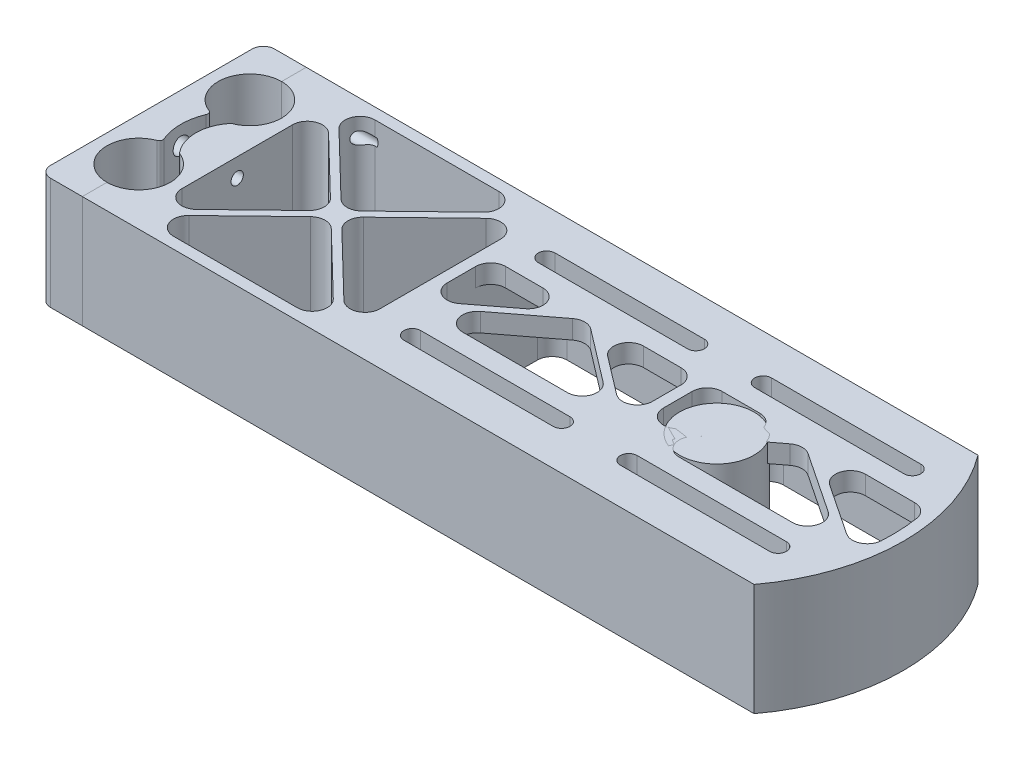
SolidWorks part; units mm, degrees
material "Сплав 2024"
ref_plane "Front" through (0, 0, 0) normal (0, 0, 1) x (1, 0, 0)
ref_plane "Top" through (0, 0, 0) normal (0, 1, 0) x (1, 0, 0)
ref_plane "Right" through (0, 0, 0) normal (1, 0, 0) x (0, 0, -1)
sketch "Эскиз1" plane through (0, 0, 0) normal (0, 1, 0) x (1, 0, 0)
  line L0 (0, 0) -> (0, 60) construction
  line L1 (0, 60) -> (180, 60)
  line L2 (190, 60) -> (190, 0) construction
  line L3 (190, 0) -> (180, 0) construction
  line L4 (0, 30) -> (140, 30) construction
  line L5 (0, 60) -> (0, 52)
  line L6 (0, 37.8) -> (0, 22.2)
  line L7 (0, 8) -> (0, 0)
  line L8 (140, 30) -> (190, 30) construction
  line L9 (180, 60) -> (190, 60) construction
  line L10 (180, 0) -> (0, 0)
  circle A0 centre (0, 44.9) radius 7.1 construction
  circle A1 centre (0, 15.1) radius 7.1 construction
  arc A2 (0, 52) -> (0, 37.8) centre (0, 44.9) cw
  arc A3 (0, 8) -> (0, 22.2) centre (0, 15.1) ccw
  arc A4 (180, 0) -> (180, 60) centre (140, 30) ccw
  point P11 (0, 52)
  point P12 (0, 37.8)
  dimension "D2" = 14.2
  dimension "D4" = 29.8
  dimension "D8" = 50
  dimension "D1" = 60
  dimension "D3" = 15.1
  dimension "D5" = 140
  dimension "D6" = 50
  dimension "D7" = 190
extrude "Бобышка-Вытянуть1" add sketch "Эскиз1" along normal blind 30
sketch "Эскиз2" plane through (0, 30, 0) normal (0, 1, 0) x (1, 0, 0)
  line L5 (3, 3) -> (178.4708, 3)
  line L6 (3, 3) -> (178.4708, 3)
  line L12 (3, 5.4558) -> (3, 3)
  line L15 (178.4708, 57) -> (3, 57)
  line L16 (3, 57) -> (3, 54.5442)
  line L17 (3, 35.2558) -> (3, 24.7442)
  line L18 (3, 5.4558) -> (3, 3)
  line L21 (178.4708, 57) -> (3, 57)
  line L22 (3, 57) -> (3, 54.5442)
  line L23 (3, 35.2558) -> (3, 24.7442)
  arc A3 (178.4708, 3) -> (178.4708, 57) centre (140, 30) ccw
  arc A4 (3, 35.2558) -> (3, 54.5442) centre (0, 44.9) ccw
  arc A5 (3, 5.4558) -> (3, 24.7442) centre (0, 15.1) ccw
  arc A6 (3, 35.2558) -> (3, 54.5442) centre (0, 44.9) ccw
  arc A7 (3, 5.4558) -> (3, 24.7442) centre (0, 15.1) ccw
  arc A8 (178.4708, 3) -> (178.4708, 57) centre (140, 30) ccw
  dimension "D1" = 3
extrude "Вырез-Вытянуть1" cut sketch "Эскиз2" against normal through all
sketch "Temp" plane through (0, 30, 0) normal (0, 1, 0) x (1, 0, 0)
  circle A0 centre (140, 30) radius 10
  dimension "D1" = 20
extrude "Бобышка-Вытянуть2" add sketch "Temp" against normal up to surface (30 mm away) separate body up to face at (49.7088, 0, -30)
sketch "Эскиз3" plane through (0, 30, 0) normal (0, 1, 0) x (1, 0, 0)
  line L0 (178.4708, 57) -> (3, 57) construction
  line L1 (174.4166, 48) -> (134.4166, 48) construction
  line L2 (174.4166, 43.5) -> (134.4166, 43.5)
  line L3 (174.4166, 52.5) -> (134.4166, 52.5)
  line L4 (174.4166, 48) -> (183.4166, 48) construction
  line L5 (125.4166, 57) -> (125.4166, 30) construction
  line L6 (0, 30) -> (140, 30) construction
  line L7 (76.4166, 48) -> (116.4166, 48) construction
  line L8 (76.4166, 43.5) -> (116.4166, 43.5)
  line L9 (76.4166, 52.5) -> (116.4166, 52.5)
  line L10 (187, 30) -> (125.4166, 30) construction
  line L11 (76.4166, 12) -> (116.4166, 12) construction
  line L12 (76.4166, 16.5) -> (116.4166, 16.5)
  line L13 (76.4166, 7.5) -> (116.4166, 7.5)
  line L14 (174.4166, 12) -> (134.4166, 12) construction
  line L15 (174.4166, 16.5) -> (134.4166, 16.5)
  line L16 (174.4166, 7.5) -> (134.4166, 7.5)
  line L17 (68.9166, 57) -> (68.9166, 40.5)
  line L18 (68.9166, 40.5) -> (185.8121, 40.5)
  line L19 (178.4708, 57) -> (68.9166, 57)
  line L20 (76.4166, 12) -> (116.4166, 12) construction
  line L21 (76.4166, 16.5) -> (116.4166, 16.5)
  line L22 (76.4166, 7.5) -> (116.4166, 7.5)
  line L23 (174.4166, 12) -> (134.4166, 12) construction
  line L24 (174.4166, 16.5) -> (134.4166, 16.5)
  line L25 (174.4166, 7.5) -> (134.4166, 7.5)
  line L26 (68.9166, 19.5) -> (185.8121, 19.5)
  line L27 (178.4708, 3) -> (68.9166, 3)
  line L28 (68.9166, 3) -> (68.9166, 19.5)
  arc A0 (174.4166, 43.5) -> (174.4166, 52.5) centre (174.4166, 48) ccw
  arc A1 (134.4166, 52.5) -> (134.4166, 43.5) centre (134.4166, 48) ccw
  arc A2 (178.4708, 3) -> (178.4708, 57) centre (140, 30) ccw construction
  arc A3 (76.4166, 43.5) -> (76.4166, 52.5) centre (76.4166, 48) cw
  arc A4 (116.4166, 52.5) -> (116.4166, 43.5) centre (116.4166, 48) cw
  arc A5 (76.4166, 16.5) -> (76.4166, 7.5) centre (76.4166, 12) ccw
  arc A6 (116.4166, 7.5) -> (116.4166, 16.5) centre (116.4166, 12) ccw
  arc A7 (174.4166, 16.5) -> (174.4166, 7.5) centre (174.4166, 12) cw
  arc A8 (134.4166, 7.5) -> (134.4166, 16.5) centre (134.4166, 12) cw
  arc A9 (185.8121, 40.5) -> (178.4708, 57) centre (140, 30) ccw
  arc A10 (76.4166, 16.5) -> (76.4166, 7.5) centre (76.4166, 12) ccw
  arc A11 (116.4166, 7.5) -> (116.4166, 16.5) centre (116.4166, 12) ccw
  arc A12 (174.4166, 16.5) -> (174.4166, 7.5) centre (174.4166, 12) cw
  arc A13 (134.4166, 7.5) -> (134.4166, 16.5) centre (134.4166, 12) cw
  arc A14 (185.8121, 19.5) -> (178.4708, 3) centre (140, 30) cw
  point P1 (154.4166, 48)
  point P20 (96.4166, 48)
  point P28 (96.4166, 12)
  point P35 (154.4166, 12)
  arc M3 (178.4708, 57) -> (178.4708, 3) centre (140, 30) cw
  line M4 (178.4708, 3) -> (3, 3)
  line M10 (3, 57) -> (178.4708, 57)
  dimension "D1" = 4.5
  dimension "D6" = 3
  dimension "D2" = 40
  dimension "D3" = 9
  dimension "D4" = 9
  dimension "D5" = 9
  dimension "D7" = 7.5
extrude "Бобышка-Вытянуть3" add sketch "Эскиз3" against normal blind 5 contours L17 L18 A1 L3 A0 L2 L9 A4 L8 A3 M3 M10 | L28 L26 A6 L13 A5 L12 L16 A8 L15 A7 M4 M3
sketch "Эскиз4" plane through (0, 30, 0) normal (0, 1, 0) x (1, 0, 0)
  line L0 (3, 57) -> (3, 54.5442) construction
  line L1 (3, 35.2558) -> (3, 24.7442) construction
  line L2 (3, 5.4558) -> (3, 3) construction
  line L3 (3, 3) -> (68.9166, 3) construction
  line L4 (68.9166, 57) -> (3, 57) construction
  line L5 (3, 57) -> (3, 54.5442)
  line L6 (3, 35.2558) -> (3, 24.7442)
  line L7 (3, 5.4558) -> (3, 3)
  line L8 (3, 3) -> (10.1, 3)
  line L9 (10.1, 57) -> (3, 57)
  line L10 (10.1, 57) -> (10.1, 3)
  arc A0 (3, 35.2558) -> (3, 54.5442) centre (0, 44.9) ccw construction
  arc A1 (3, 5.4558) -> (3, 24.7442) centre (0, 15.1) ccw construction
  arc A2 (3, 35.2558) -> (3, 54.5442) centre (0, 44.9) ccw
  arc A3 (3, 5.4558) -> (3, 24.7442) centre (0, 15.1) ccw
  line M4 (68.9166, 3) -> (3, 3)
  line M5 (3, 3) -> (3, 5.4558)
  arc M6 (3, 5.4558) -> (3, 24.7442) centre (0, 15.1) ccw
  line M7 (3, 24.7442) -> (3, 35.2558)
  arc M8 (3, 35.2558) -> (3, 54.5442) centre (0, 44.9) ccw
  line M9 (3, 54.5442) -> (3, 57)
  line M10 (3, 57) -> (68.9166, 57)
extrude "Бобышка-Вытянуть4" add sketch "Эскиз4" against normal through all contours L10 M10 M9 M8 | L10 M8 M7 M6 | L10 M6 M5 M4
sketch "Эскиз6" plane through (0, 30, 0) normal (0, 1, 0) x (1, 0, 0)
  line L0 (65.9166, 57) -> (65.9166, 3)
  line L1 (68.9166, 57) -> (10.1, 57) construction
  line L2 (10.1, 3) -> (68.9166, 3) construction
  line L3 (68.9166, 57) -> (68.9166, 40.5) construction
  line L4 (65.9166, 3) -> (68.9166, 3)
  line L5 (68.9166, 3) -> (68.9166, 57)
  line L6 (68.9166, 57) -> (65.9166, 57)
  dimension "D1" = 3
extrude "Бобышка-Вытянуть5" add sketch "Эскиз6" against normal through all
sketch "Эскиз7" plane through (0, 30, 0) normal (0, 1, 0) x (1, 0, 0)
  line L0 (10.1, 3) -> (65.9166, 57) construction
  line L1 (10.1, 57) -> (65.9166, 3) construction
  line L2 (10.1, 55.6086) -> (36.5701, 30)
  line L3 (11.5382, 3) -> (38.0083, 28.6086)
  line L4 (11.5382, 57) -> (38.0083, 31.3914)
  line L5 (10.1, 4.3914) -> (36.5701, 30)
  line L6 (65.9166, 57) -> (10.1, 57) construction
  line L7 (10.1, 57) -> (10.1, 3) construction
  line L8 (10.1, 3) -> (65.9166, 3) construction
  line L9 (65.9166, 57) -> (65.9166, 3) construction
  line L10 (65.9166, 57) -> (64.4784, 57)
  line L11 (10.1, 57) -> (10.1, 55.6086)
  line L12 (10.1, 3) -> (11.5382, 3)
  line L13 (65.9166, 57) -> (65.9166, 55.6086)
  line L14 (11.5382, 57) -> (10.1, 57)
  line L15 (10.7953, 57.7187) -> (66.6119, 3.7187) construction
  line L16 (9.4047, 56.2813) -> (65.2213, 2.2813) construction
  line L17 (65.9166, 4.3914) -> (65.9166, 3)
  line L18 (9.4047, 3.7187) -> (65.2213, 57.7187) construction
  line L19 (10.7953, 2.2813) -> (66.6119, 56.2813) construction
  line L20 (64.4784, 3) -> (65.9166, 3)
  line L21 (10.1, 4.3914) -> (10.1, 3)
  line L22 (39.4465, 30) -> (65.9166, 55.6086)
  line L23 (39.4465, 30) -> (65.9166, 4.3914)
  line L24 (38.0083, 31.3914) -> (64.4784, 57)
  line L25 (38.0083, 28.6086) -> (64.4784, 3)
  dimension "D1" = 1
  dimension "D2" = 1
extrude "Бобышка-Вытянуть6" add sketch "Эскиз7" against normal through all
sketch "Эскиз9" plane through (0, 25, 0) normal (0, -1, 0) x (1, 0, 0)
  line L0 (120.9166, -12) -> (129.9166, -12) construction
  line L1 (125.4166, -3) -> (125.4166, -57) construction
  line L2 (68.9166, -57) -> (178.4708, -57) construction
  line L3 (123.9166, -3) -> (123.9166, -57)
  line L4 (101.5292, -3) -> (68.9166, -3) construction
  line L5 (126.9166, -3) -> (126.9166, -57)
  line L6 (123.9166, -3) -> (126.9166, -3)
  line L7 (123.9166, -57) -> (126.9166, -57)
  arc A0 (116.4166, -16.5) -> (116.4166, -7.5) centre (116.4166, -12) ccw construction
  arc A1 (134.4166, -16.5) -> (134.4166, -7.5) centre (134.4166, -12) ccw construction
  point P8 (125.4166, -12)
  dimension "D1" = 1.5
  dimension "D2" = 1.5
extrude "Бобышка-Вытянуть8" add sketch "Эскиз9" along normal through all and the other way through all
sketch "Эскиз8" plane through (0, 30, 0) normal (0, 1, 0) x (1, 0, 0)
  line L0 (96.4166, 43.5) -> (96.4166, 16.5) construction
  line L1 (76.4166, 43.5) -> (116.4166, 43.5) construction
  line L2 (76.4166, 16.5) -> (116.4166, 16.5) construction
  line L3 (154.4166, 43.5) -> (154.4166, 16.5) construction
  line L4 (174.4166, 43.5) -> (134.4166, 43.5) construction
  line L5 (174.4166, 16.5) -> (134.4166, 16.5) construction
  line L6 (68.9166, 19.5) -> (96.4166, 40.5) construction
  line L7 (116.4166, 48) -> (134.4166, 48) construction
  line L8 (125.4166, 48) -> (125.4166, 19.5) construction
  line L9 (68.9166, 40.5) -> (123.9166, 40.5) construction
  line L10 (96.4166, 40.5) -> (123.9166, 19.5) construction
  line L11 (126.9166, 19.5) -> (154.4401, 40.4052) construction
  line L12 (154.4401, 40.4052) -> (185.8121, 19.5) construction
  line L13 (70.5643, 19.5) -> (96.4166, 39.2418)
  line L14 (96.4166, 39.2418) -> (122.2689, 19.5)
  line L15 (128.5699, 19.5) -> (154.478, 39.1782)
  line L16 (154.478, 39.1782) -> (184.0088, 19.5)
  line L17 (68.9166, 20.7582) -> (94.7689, 40.5)
  line L18 (98.0643, 40.5) -> (123.9166, 20.7582)
  line L19 (126.9166, 20.7557) -> (152.9116, 40.5)
  line L20 (122.2689, 19.5) -> (123.9166, 19.5)
  line L22 (94.7689, 40.5) -> (98.0643, 40.5)
  line L23 (68.9166, 19.5) -> (68.9166, 40.5) construction
  line L24 (68.9166, 19.5) -> (123.9166, 19.5) construction
  line L25 (123.9166, 19.5) -> (123.9166, 40.5) construction
  line L26 (126.9166, 40.5) -> (126.9166, 19.5) construction
  line L27 (126.9166, 40.5) -> (185.8121, 40.5) construction
  line L28 (126.9166, 19.5) -> (185.8121, 19.5) construction
  line L29 (68.9166, 19.5) -> (68.9166, 20.7582)
  line L30 (68.9166, 19.5) -> (70.5643, 19.5)
  line L31 (123.9166, 19.5) -> (123.9166, 20.7582)
  line L32 (126.9166, 20.7557) -> (126.9166, 19.5)
  line L33 (152.9116, 40.5) -> (156.1011, 40.5)
  line L34 (126.9166, 19.5) -> (128.5699, 19.5)
  line L35 (184.0088, 19.5) -> (185.8121, 19.5)
  line L36 (154.4021, 41.6321) -> (186.3666, 20.3322) construction
  line L37 (154.478, 39.1782) -> (185.2576, 18.6678) construction
  line L38 (156.1011, 40.5) -> (186.0401, 20.5497)
  line L39 (127.5214, 18.7037) -> (154.478, 39.1782) construction
  line L40 (126.3117, 20.2963) -> (154.4021, 41.6321) construction
  line L42 (96.4166, 41.7582) -> (124.5235, 20.2948) construction
  line L43 (68.3097, 20.2948) -> (96.4166, 41.7582) construction
  line L44 (69.5235, 18.7052) -> (96.4166, 39.2418) construction
  line L45 (96.4166, 39.2418) -> (123.3097, 18.7052) construction
  arc A1 (185.8121, 19.5) -> (185.8121, 40.5) centre (140, 30) ccw construction
  arc A2 (185.8121, 19.5) -> (186.0401, 20.5497) centre (140, 30) ccw
  point P26 (69.5235, 18.7052)
  point P27 (96.4324, 39.2539)
  point P28 (125.4324, 18.2539)
  point P30 (185.2357, 18.6828)
  point P31 (68.3097, 20.2948)
  point P32 (96.4007, 41.7461)
  point P33 (125.4007, 20.7461)
  point P34 (154.3931, 42.8858)
  point P35 (186.3885, 20.3172)
  point P49 (154.4166, 40.5)
  dimension "D1" = 1
  dimension "D2" = 1
extrude "Бобышка-Вытянуть7" add sketch "Эскиз8" against normal up to surface (5 mm away) up to face at (96.4166, 25, -12)
fillet "Скругление1" radius 4 10 edges at (11.5382, 15, -57) (38.0083, 15, -31.3914) (64.4784, 15, -57) (65.9166, 15, -55.6086) (39.4465, 15, -30) (65.9166, 15, -4.3914) (11.5382, 15, -3) (64.4784, 15, -3) (38.0083, 15, -28.6086) (36.5701, 15, -30)
fillet "Скругление2" radius 4 8 edges at (178.4708, 12.5, -57) (178.4708, 12.5, -3) (126.9166, 12.5, -3) (126.9166, 12.5, -57) (123.9166, 12.5, -3) (68.9166, 12.5, -3) (68.9166, 12.5, -57) (123.9166, 12.5, -57)
fillet "Скругление3" radius 4 18 edges at (98.0643, 27.5, -40.5) (123.9166, 27.5, -40.5) (123.9166, 27.5, -20.7582) (122.2689, 27.5, -19.5) (96.4166, 27.5, -39.2418) (70.5643, 27.5, -19.5) (94.7689, 27.5, -40.5) (68.9166, 27.5, -40.5) (68.9166, 27.5, -20.7582) (185.8121, 27.5, -40.5) (156.1011, 27.5, -40.5) (186.0401, 27.5, -20.5497) (184.0088, 27.5, -19.5) (154.478, 27.5, -39.1782) (128.5699, 27.5, -19.5) (126.9166, 27.5, -20.7557) (152.9116, 27.5, -40.5) (126.9166, 27.5, -40.5)
sketch "Эскиз10" plane through (0, 30, 0) normal (0, 1, 0) x (1, 0, 0)
  line L90 (76.4166, 52.5) -> (116.4166, 52.5) construction
  line L91 (76.4166, 43.5) -> (116.4166, 43.5) construction
  line L92 (116.4166, 50.25) -> (76.4166, 50.25)
  line L93 (76.4166, 45.75) -> (116.4166, 45.75)
  line L94 (116.4166, 50.25) -> (76.4166, 50.25)
  line L95 (76.4166, 45.75) -> (116.4166, 45.75)
  line L96 (76.4166, 52.5) -> (116.4166, 52.5)
  line L97 (76.4166, 43.5) -> (116.4166, 43.5)
  line L98 (174.4166, 52.5) -> (134.4166, 52.5) construction
  line L99 (174.4166, 43.5) -> (134.4166, 43.5) construction
  line L100 (174.4166, 52.5) -> (134.4166, 52.5)
  line L101 (174.4166, 43.5) -> (134.4166, 43.5)
  line L102 (76.4166, 16.5) -> (116.4166, 16.5) construction
  line L103 (76.4166, 7.5) -> (116.4166, 7.5) construction
  line L104 (76.4166, 16.5) -> (116.4166, 16.5)
  line L105 (76.4166, 7.5) -> (116.4166, 7.5)
  line L106 (174.4166, 16.5) -> (134.4166, 16.5) construction
  line L107 (174.4166, 7.5) -> (134.4166, 7.5) construction
  line L108 (174.4166, 16.5) -> (134.4166, 16.5)
  line L109 (174.4166, 7.5) -> (134.4166, 7.5)
  line L110 (174.4166, 45.75) -> (134.4166, 45.75)
  line L111 (174.4166, 50.25) -> (134.4166, 50.25)
  line L112 (174.4166, 14.25) -> (134.4166, 14.25)
  line L113 (174.4166, 9.75) -> (134.4166, 9.75)
  line L114 (76.4166, 9.75) -> (116.4166, 9.75)
  line L115 (76.4166, 14.25) -> (116.4166, 14.25)
  arc A90 (76.4166, 52.5) -> (76.4166, 43.5) centre (76.4166, 48) ccw construction
  arc A91 (116.4166, 43.5) -> (116.4166, 52.5) centre (116.4166, 48) ccw construction
  arc A92 (76.4166, 50.25) -> (76.4166, 45.75) centre (76.4166, 48) ccw
  arc A93 (116.4166, 45.75) -> (116.4166, 50.25) centre (116.4166, 48) ccw
  arc A94 (76.4166, 50.25) -> (76.4166, 45.75) centre (76.4166, 48) ccw
  arc A95 (116.4166, 45.75) -> (116.4166, 50.25) centre (116.4166, 48) ccw
  arc A96 (76.4166, 52.5) -> (76.4166, 43.5) centre (76.4166, 48) ccw
  arc A97 (116.4166, 43.5) -> (116.4166, 52.5) centre (116.4166, 48) ccw
  arc A98 (134.4166, 52.5) -> (134.4166, 43.5) centre (134.4166, 48) ccw construction
  arc A99 (174.4166, 43.5) -> (174.4166, 52.5) centre (174.4166, 48) ccw construction
  arc A100 (134.4166, 52.5) -> (134.4166, 43.5) centre (134.4166, 48) ccw
  arc A101 (174.4166, 43.5) -> (174.4166, 52.5) centre (174.4166, 48) ccw
  arc A102 (116.4166, 7.5) -> (116.4166, 16.5) centre (116.4166, 12) ccw construction
  arc A103 (76.4166, 16.5) -> (76.4166, 7.5) centre (76.4166, 12) ccw construction
  arc A104 (116.4166, 7.5) -> (116.4166, 16.5) centre (116.4166, 12) ccw
  arc A105 (76.4166, 16.5) -> (76.4166, 7.5) centre (76.4166, 12) ccw
  arc A106 (134.4166, 16.5) -> (134.4166, 7.5) centre (134.4166, 12) ccw construction
  arc A107 (174.4166, 7.5) -> (174.4166, 16.5) centre (174.4166, 12) ccw construction
  arc A108 (134.4166, 16.5) -> (134.4166, 7.5) centre (134.4166, 12) ccw
  arc A109 (174.4166, 7.5) -> (174.4166, 16.5) centre (174.4166, 12) ccw
  arc A110 (134.4166, 50.25) -> (134.4166, 45.75) centre (134.4166, 48) ccw
  arc A111 (174.4166, 45.75) -> (174.4166, 50.25) centre (174.4166, 48) ccw
  arc A112 (134.4166, 14.25) -> (134.4166, 9.75) centre (134.4166, 12) ccw
  arc A113 (174.4166, 9.75) -> (174.4166, 14.25) centre (174.4166, 12) ccw
  arc A114 (76.4166, 14.25) -> (76.4166, 9.75) centre (76.4166, 12) ccw
  arc A115 (116.4166, 9.75) -> (116.4166, 14.25) centre (116.4166, 12) ccw
  dimension "D1" = 2.25
  dimension "D2" = 2.25
  dimension "D3" = 2.25
  dimension "D4" = 2.25
extrude "Бобышка-Вытянуть9" add sketch "Эскиз10" against normal up to surface (5 mm away) up to face at (155.2427, 25, -27.7696)
sketch "Эскиз12" plane through (0, 0, 0) normal (0, -1, 0) x (1, 0, 0)
  line L0 (5, -23.8755) -> (5, -36.1245)
  line L1 (0, -37.8) -> (0, -22.2) construction
  line L2 (10.1, -55.6086) -> (10.1, -4.3914) construction
  line L3 (10.1, -44.9) -> (10.1, -15.1)
  arc A6 (0, -25.2) -> (0, -5) centre (0, -15.1) ccw
  arc A7 (5, -23.8755) -> (10.1, -15.1) centre (0, -15.1) ccw
  arc A9 (0, -55) -> (0, -34.8) centre (0, -44.9) ccw
  arc A10 (10.1, -44.9) -> (5, -36.1245) centre (0, -44.9) ccw
  dimension "D3" = 5
  dimension "D1" = 3
  dimension "D2" = 3
extrude "Вырез-Вытянуть2" [suppressed] cut sketch "Эскиз12" against normal through all
sketch "Эскиз15" [suppressed] plane through (0, 0, 0) normal (0, -1, 0) x (1, 0, 0)
  line L5 (180, 0) -> (0, 0)
  line L6 (0, 0) -> (0, -8)
  line L7 (0, -22.2) -> (0, -37.8)
  line L8 (0, -52) -> (0, -60)
  line L9 (0, -60) -> (180, -60)
  line L10 (180, 0) -> (0, 0)
  line L11 (0, 0) -> (0, -8)
  line L12 (0, -22.2) -> (0, -37.8)
  line L13 (0, -52) -> (0, -60)
  line L14 (0, -60) -> (180, -60)
  arc A3 (0, -22.2) -> (0, -8) centre (0, -15.1) ccw
  arc A4 (0, -52) -> (0, -37.8) centre (0, -44.9) ccw
  arc A5 (180, -60) -> (180, 0) centre (140, -30) ccw
  arc A6 (0, -22.2) -> (0, -8) centre (0, -15.1) ccw
  arc A7 (0, -52) -> (0, -37.8) centre (0, -44.9) ccw
  arc A8 (180, -60) -> (180, 0) centre (140, -30) ccw
  dimension "D1" = 0
extrude "Вырез-Вытянуть3" [suppressed] cut sketch "Эскиз15" against normal blind 20
split "Разделить1" [suppressed] bodies to split 113
move or copy body "Тело-Переместить/Копировать1" [suppressed] bodies to move or copy 116 placed by mates yes
other "Расстояние2" [suppressed] parameters "D1"=50
sketch "Эскиз16" plane through (0, 30, 0) normal (0, 1, 0) x (1, 0, 0)
  line L0 (0, 8) -> (0, 0) construction
  line L1 (0, 37.8) -> (0, 22.2) construction
  line L2 (0, 60) -> (0, 52) construction
  line L3 (0, 8) -> (0, 6.6)
  line L4 (0, 37.8) -> (0, 36.4)
  line L5 (0, 53.4) -> (0, 52)
  line L6 (0, 23.6) -> (0, 22.2)
  arc A3 (0, 36.4) -> (0, 53.4) centre (0, 44.9) ccw
  arc A4 (0, 36.4) -> (0, 53.4) centre (0, 44.9) ccw
  arc A5 (0, 37.8) -> (0, 52) centre (0, 44.9) ccw construction
  arc A6 (0, 6.6) -> (0, 23.6) centre (0, 15.1) ccw
  arc A7 (0, 6.6) -> (0, 23.6) centre (0, 15.1) ccw
  arc A8 (0, 8) -> (0, 22.2) centre (0, 15.1) ccw construction
  arc A9 (0, 37.8) -> (0, 52) centre (0, 44.9) ccw
  arc A10 (0, 8) -> (0, 22.2) centre (0, 15.1) ccw
  dimension "D1" = 1.4
  dimension "D2" = 1.4
extrude "Вырез-Вытянуть4" cut sketch "Эскиз16" against normal through all
sketch "Эскиз17" plane through (0, 30, 0) normal (0, 1, 0) x (1, 0, 0)
  line L1 (10.1, 55.6086) -> (10.1, 4.3914) construction
  line L2 (11.5, 55.6086) -> (11.5, 4.3914)
  line L3 (11.5, 54.2542) -> (11.5, 5.7458)
  line L4 (10.1, 55.6086) -> (33.5986, 32.8748) construction
  line L5 (33.5986, 27.1252) -> (10.1, 4.3914) construction
  line L6 (10.1, 55.6086) -> (10.1, 4.3914)
  line L7 (10.1, 55.6086) -> (11.5, 54.2542)
  line L8 (11.5, 5.7458) -> (10.1, 4.3914)
  dimension "D1" = 1.4
extrude "Бобышка-Вытянуть10" add sketch "Эскиз17" against normal through all
fillet "Скругление4" radius 4 2 edges at (11.5, 15, -54.2542) (11.5, 15, -5.7458)
hole_wizard "Отверстие обработанное метчиком M4x0.71" positions "Эскиз13" profile "Эскиз14" tap size "M4x0.7" standard "Ansi Metric"
sketch "Эскиз13" plane through (0, -175.3797, -75.0604) normal (-1, 0, 0) x (0, 0, 1)
  point P0 (19.3104, 200.3797)
  point P3 (45.0604, 200.3797)
  point P6 (70.8104, 200.3797)
  point P9 (70.8104, 180.3797)
  point P12 (45.0604, 180.3797)
  point P15 (19.3104, 180.3797)
sketch "Эскиз14" plane through (0, 25, -55.75) normal (0, 1, 0) x (0, 0, 1)
  line L0 (0, 0) -> (0, 22.9914)
  line L1 (0, 22.9914) -> (1.65, 22)
  line L2 (1.65, 22) -> (1.65, 0)
  line L3 (1.65, 0) -> (0, 0)
  line L4 (0, 22.9914) -> (-1.65, 22) construction
  line L5 (0, -6.35) -> (0, 107.95) construction
  dimension "Диаметр сверла" = 3.3
  dimension "Глубина сверла" = 22
  dimension "Угол заточки сверла" = 118
cosmetic thread "Отверстие резьбы4" parameters "D1"=22, "D2"=4
cosmetic thread "Отверстие резьбы5" parameters "D1"=11.5, "D2"=4
cosmetic thread "Отверстие резьбы6" parameters "D1"=22, "D2"=4
cosmetic thread "Отверстие резьбы7" parameters "D1"=22, "D2"=4
cosmetic thread "Отверстие резьбы8" parameters "D1"=22, "D2"=4
cosmetic thread "Отверстие резьбы9" parameters "D1"=22, "D2"=4
fillet "Скругление5" [suppressed] radius 1
sketch "Эскиз18" plane through (0, 0, 0) normal (0, -1, 0) x (1, 0, 0)
  line L0 (0, -6.6) -> (0, -23.6) construction
  line L1 (0, -6.6) -> (0, 0)
  line L3 (-11.5, -15.1) -> (-11.5, 0)
  line L4 (-11.5, -44.9) -> (-11.5, -60)
  line L5 (0, -60) -> (0, -53.4)
  line L6 (0, -36.4) -> (0, -23.6)
  line L7 (-11.5, -15.1) -> (-11.5, -44.9) construction
  line L8 (0, -36.4) -> (0, -53.4) construction
  line L9 (-6.5, -24.5868) -> (-6.5, -35.4132)
  line L10 (-11.5, -60) -> (0, -60)
  line L12 (-11.5, 0) -> (0, 0)
  arc A0 (-11.5, -44.9) -> (-6.5, -35.4132) centre (0, -44.9) cw
  arc A1 (-6.5, -24.5868) -> (-11.5, -15.1) centre (0, -15.1) cw
  arc A4 (0, -53.4) -> (0, -36.4) centre (0, -44.9) cw
  arc A5 (0, -23.6) -> (0, -6.6) centre (0, -15.1) cw
  point P4 (-3, -56.0018)
  point P7 (-3, -33.7982)
  point P14 (-3, -26.2018)
  point P16 (-3, -3.9982)
  point P22 (-11.5, -15.1)
  point P23 (-11.5, -44.9)
  dimension "D3" = 8.5
  dimension "D2" = 8.5
  dimension "D4" = 5
  dimension "D1" = 3
  dimension "D5" = 11.5
  dimension "D6" = 11.5
  dimension "D7" = 3
extrude "Бобышка-Вытянуть11" add sketch "Эскиз18" against normal through all separate body
sketch "Эскиз21" plane through (0, 0, 0) normal (0, -1, 0) x (1, 0, 0)
  line L0 (-11.5, -15.1) -> (-11.5, -44.9)
  line L1 (-11.5, -44.9) -> (-10.1735, -44.9)
  line L2 (-10.1735, -44.9) -> (-4.7554, -34.2235)
  line L3 (-4.7554, -34.2235) -> (-4.7554, -23.6234)
  line L4 (-4.7554, -23.6234) -> (-11.5, -15.1)
  arc A0 (-6.5, -35.4132) -> (-11.5, -44.9) centre (0, -44.9) ccw construction
extrude "Бобышка-Вытянуть12" add sketch "Эскиз21" against normal through all
sketch "Эскиз22" plane through (0, 0, 0) normal (0, -1, 0) x (1, 0, 0)
  line L0 (-2, -23.3614) -> (-2, -36.6386) construction
  line L1 (0, -36.4) -> (0, -23.6) construction
  arc A0 (0, -6.6) -> (0, -23.6) centre (0, -15.1) ccw construction
  arc A1 (0, -36.4) -> (0, -53.4) centre (0, -44.9) ccw construction
  arc A2 (-2, -36.6386) -> (-2, -23.3614) centre (11.0946, -30) cw
  arc A3 (2.9722, -36.9366) -> (2.9722, -23.0634) centre (11.0946, -30) cw
  arc A4 (0, -23.6) -> (0, -6.6) centre (0, -15.1) ccw construction
  arc A5 (0, -53.4) -> (0, -36.4) centre (0, -44.9) ccw construction
  arc A6 (0, -23.6) -> (2.9722, -23.0634) centre (0, -15.1) ccw
  arc A7 (2.9722, -36.9366) -> (0, -36.4) centre (0, -44.9) ccw
  arc A8 (1.5677, -34.8299) -> (1.5677, -25.1701) centre (11.0946, -30) cw construction
  arc A9 (-2, -23.3614) -> (0, -23.6) centre (0, -15.1) ccw
  arc A10 (0, -36.4) -> (-2, -36.6386) centre (0, -44.9) ccw
  dimension "D2" = 13.2773
  dimension "D3" = 13.7773
  dimension "D1" = 2
  dimension "D4" = 4
extrude "Вырез-Вытянуть6" cut sketch "Эскиз22" against normal through all
sketch "Эскиз23" [suppressed] plane through (0, 0, 0) normal (0, -1, 0) x (1, 0, 0)
  line L0 (-2, -23.3614) -> (-2, -36.6386)
  line L1 (0, -36.4) -> (0, -23.6) construction
  line L2 (2, -23.3614) -> (2, -37.1432)
  arc A0 (0, -6.6) -> (0, -23.6) centre (0, -15.1) ccw construction
  arc A1 (0, -36.4) -> (0, -53.4) centre (0, -44.9) ccw construction
  arc A2 (0, -23.6) -> (0, -6.6) centre (0, -15.1) ccw construction
  arc A3 (0, -53.4) -> (0, -36.4) centre (0, -44.9) ccw construction
  arc A4 (0, -36.4) -> (-2, -36.6386) centre (0, -44.9) ccw
  arc A5 (-2, -23.3614) -> (0, -23.6) centre (0, -15.1) ccw
  arc A6 (0, -23.6) -> (2, -23.3614) centre (0, -15.1) ccw
  arc A7 (2, -36.6386) -> (0, -36.4) centre (0, -44.9) ccw
  dimension "D1" = 2
  dimension "D2" = 4
extrude "Вырез-Вытянуть7" [suppressed] cut sketch "Эскиз23" against normal through all
fillet "Скругление8" radius 1 2 edges at (-2, 15, -36.6386) (-2, 15, -23.3614)
fillet "Скругление9" radius 1 2 edges at (2.9722, 15, -36.9366) (2.9722, 15, -23.0634)
hole_wizard "Цековка для винта с внутренним шестигранником M41" positions "Эскиз25" profile "Эскиз24" counterbore size "M4" standard "Ansi Metric"
sketch "Эскиз25" plane through (-11.5, 0, 0) normal (-1, 0, 0) x (0, 0, 1)
  point P0 (-30, 5)
  point P3 (-30, 25)
sketch "Эскиз24" plane through (-11.5, 5, -30) normal (0, 1, 0) x (0, 0, 1)
  line L0 (0, 0) -> (0, 10.3519)
  line L1 (0, 10.3519) -> (2.25, 9)
  line L2 (2.25, 9) -> (2.25, 4)
  line L3 (2.25, 4) -> (4, 4)
  line L4 (4, 4) -> (4, 0)
  line L5 (4, 0) -> (0, 0)
  line L10 (0, 10.3519) -> (-2.25, 9) construction
  line L11 (0, -6.35) -> (0, 107.95) construction
  dimension "Диаметр отверстия" = 4.5
  dimension "Глубина отверстия" = 9
  dimension "Диаметр цековки" = 8
  dimension "Глубина цековки" = 4
  dimension "Угол заточки сверла" = 118
fillet "Скругление10" radius 3 2 edges at (-11.5, 15, 0) (-11.5, 15, -60)
equation "\"D3@Эскиз1\"=8+\"D2@Эскиз1\"/2"
equation "\"D7@Эскиз3\"=\"D1@Эскиз3\"+3"
equation "\"Утопление\"= 5"
equation "\"D4@Эскиз18\"=\"Утопление\""
equation "\"D3@Эскиз22\"=\"D2@Эскиз22\"+0.5"
equation "\"D2@Эскиз23\"=\"D1@Эскиз23\"*2"
